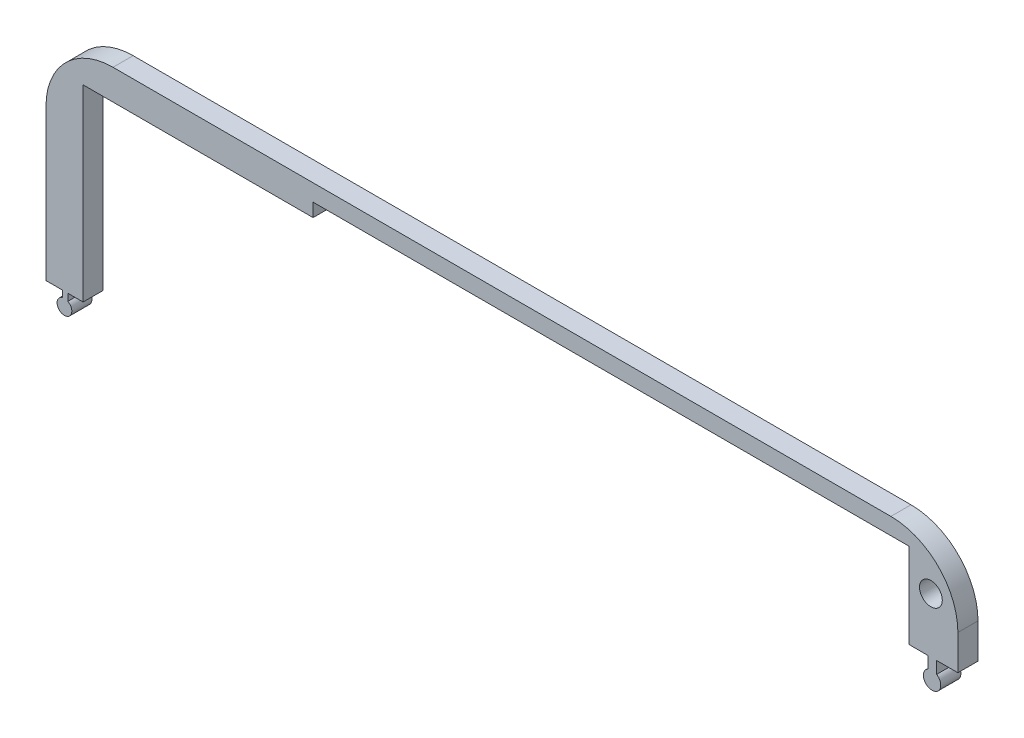
SolidWorks part; units mm, degrees
ref_plane "Front Plane" through (0, 0, 0) normal (0, 0, 1) x (1, 0, 0)
ref_plane "Top Plane" through (0, 0, 0) normal (0, 1, 0) x (1, 0, 0)
ref_plane "Right Plane" through (0, 0, 0) normal (1, 0, 0) x (0, 0, -1)
sketch "Sketch1" plane through (0, 0, 0) normal (0, 0, 1) x (1, 0, 0)
  line L8 (-93.5366, 73.7988) -> (22.5267, 73.7988)
  line L9 (32.5267, 83.7988) -> (32.5267, 133.7988)
  line L10 (22.5267, 143.7988) -> (-93.5366, 143.7988)
  line L11 (-103.5366, 133.7988) -> (-103.5366, 83.7988)
  line L24 (7.2413, 79.1138) -> (7.2413, 115.2988)
  line L25 (7.2413, 115.2988) -> (25.2005, 115.2988)
  line L26 (25.2005, 115.2988) -> (25.2005, 141.2988)
  line L27 (25.2005, 141.2988) -> (-63.6861, 141.2988)
  line L28 (-63.6861, 141.2988) -> (-63.6861, 139.2988)
  line L29 (-63.6861, 139.2988) -> (-98, 139.2988)
  line L30 (-98, 139.2988) -> (-98, 79.1138)
  line L31 (-98, 79.1138) -> (7.2413, 79.1138)
  arc A8 (22.5267, 73.7988) -> (32.5267, 83.7988) centre (22.5267, 83.7988) ccw
  arc A9 (32.5267, 133.7988) -> (22.5267, 143.7988) centre (22.5267, 133.7988) ccw
  arc A10 (-93.5366, 143.7988) -> (-103.5366, 133.7988) centre (-93.5366, 133.7988) ccw
  arc A11 (-103.5366, 83.7988) -> (-93.5366, 73.7988) centre (-93.5366, 83.7988) ccw
extrude "Boss-Extrude1" add sketch "Sketch1" along normal blind 3
sketch "Sketch2" plane through (0, 0, 3) normal (0, 0, 1) x (1, 0, 0)
  line L0 (-98, 111.233) -> (-100.276, 111.233)
  line L1 (-101.1106, 111.233) -> (-103.5366, 111.233)
  line L2 (-101.1106, 110.2573) -> (-101.1106, 111.233)
  line L3 (28.0964, 126.8564) -> (28.0964, 128.5916)
  line L4 (-100.276, 110.1813) -> (-100.276, 111.233)
  line L5 (-98, 139.2988) -> (-98, 79.1138) construction
  line L6 (-103.5366, 133.7988) -> (-103.5366, 83.7988) construction
  line L7 (28.0964, 128.5916) -> (25.2005, 128.5916)
  line L8 (25.2005, 115.2988) -> (25.2005, 141.2988) construction
  line L9 (32.5267, 128.5916) -> (29.357, 128.5916)
  line L10 (32.5267, 83.7988) -> (32.5267, 133.7988) construction
  line L11 (29.357, 128.5916) -> (29.357, 126.7956)
  line L12 (-103.5366, 111.233) -> (-103.5366, 155.1691)
  line L13 (-103.5366, 155.1691) -> (37.5209, 146.4954)
  line L14 (37.5209, 146.4954) -> (36.42, 128.5916)
  line L15 (36.42, 128.5916) -> (32.5267, 128.5916)
  line L16 (25.2005, 128.5916) -> (-98, 111.233)
  arc A0 (-101.1106, 110.2573) -> (-100.276, 110.1813) centre (-100.7855, 109.2063) ccw
  arc A1 (28.0964, 126.8564) -> (29.357, 126.7956) centre (28.6722, 125.6963) ccw
hole_wizard "M3 Clearance Hole1" positions "Sketch4" profile "Sketch3" hole size "M3" standard "ISO" end condition through all
sketch "Sketch4" plane through (0, 0, 0) normal (0, 0, -1) x (-1, 0, 0)
  point P0 (-28.4975, 136.7988)
  point P2 (-28.4975, 81.7988)
sketch "Sketch3" plane through (28.4975, 136.7988, 0) normal (1, 0, 0) x (0, 1, 0)
  line L0 (0, 0) -> (0, 3)
  line L1 (0, 3) -> (1.7, 3)
  line L2 (1.7, 3) -> (1.7, 0)
  line L5 (1.7, 0) -> (0, 0)
  line L11 (0, -6.35) -> (0, 107.95) construction
  dimension "Thru Hole Dia." = 3.4
  dimension "Thru Hole Depth" = 3
extrude "Cut-Extrude1" cut sketch "Sketch2" against normal blind 10 flip side to cut
